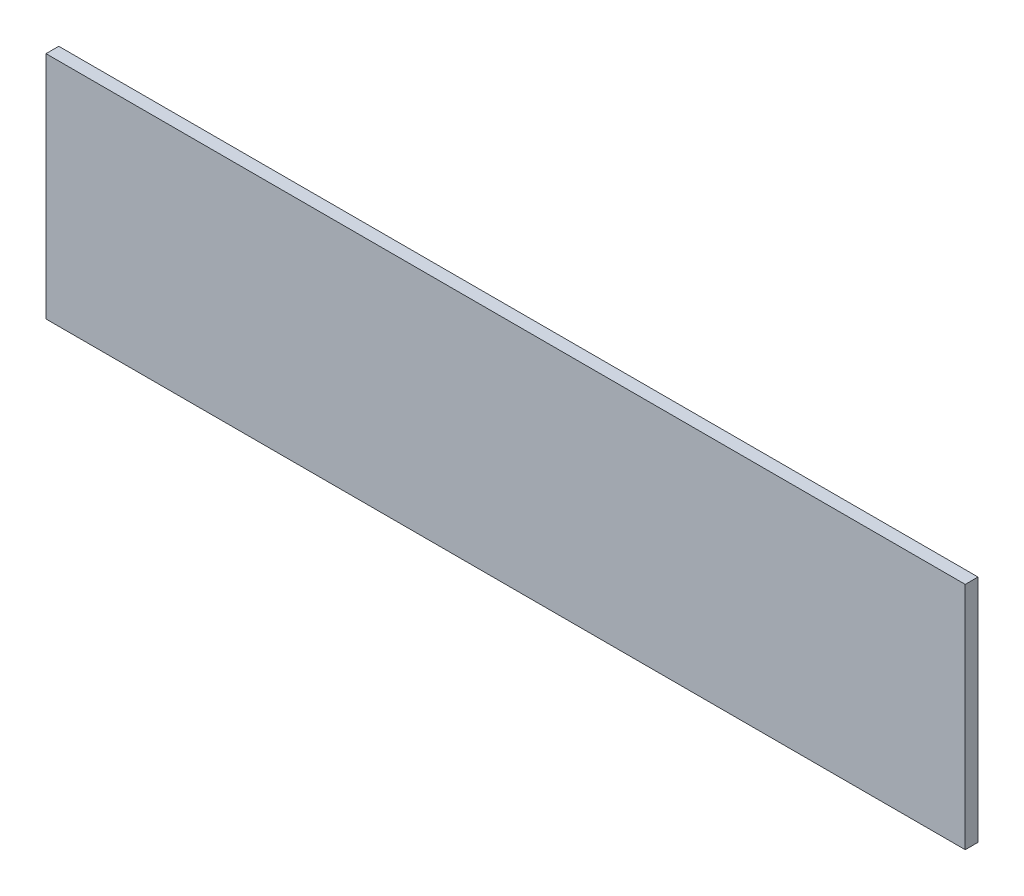
SolidWorks part; units mm, degrees
ref_plane "前视基准面" through (0, 0, 0) normal (0, 0, 1) x (1, 0, 0)
ref_plane "上视基准面" through (0, 0, 0) normal (0, 1, 0) x (1, 0, 0)
ref_plane "右视基准面" through (0, 0, 0) normal (1, 0, 0) x (0, 0, -1)
sketch "草图1" plane through (0, 0, 0) normal (0, 0, 1) x (1, 0, 0)
  line L1 (-200, 45) -> (160, 45)
  line L2 (-200, 45) -> (-200, -45)
  line L3 (-200, -45) -> (160, -45)
  line L4 (160, 45) -> (160, -45)
  line L5 (-200, 45) -> (160, -45) construction
  line L6 (-200, -45) -> (160, 45) construction
  point P0 (0, 0)
  dimension "D1" = 360
extrude "凸台-拉伸1" add sketch "草图1" along normal blind 5
